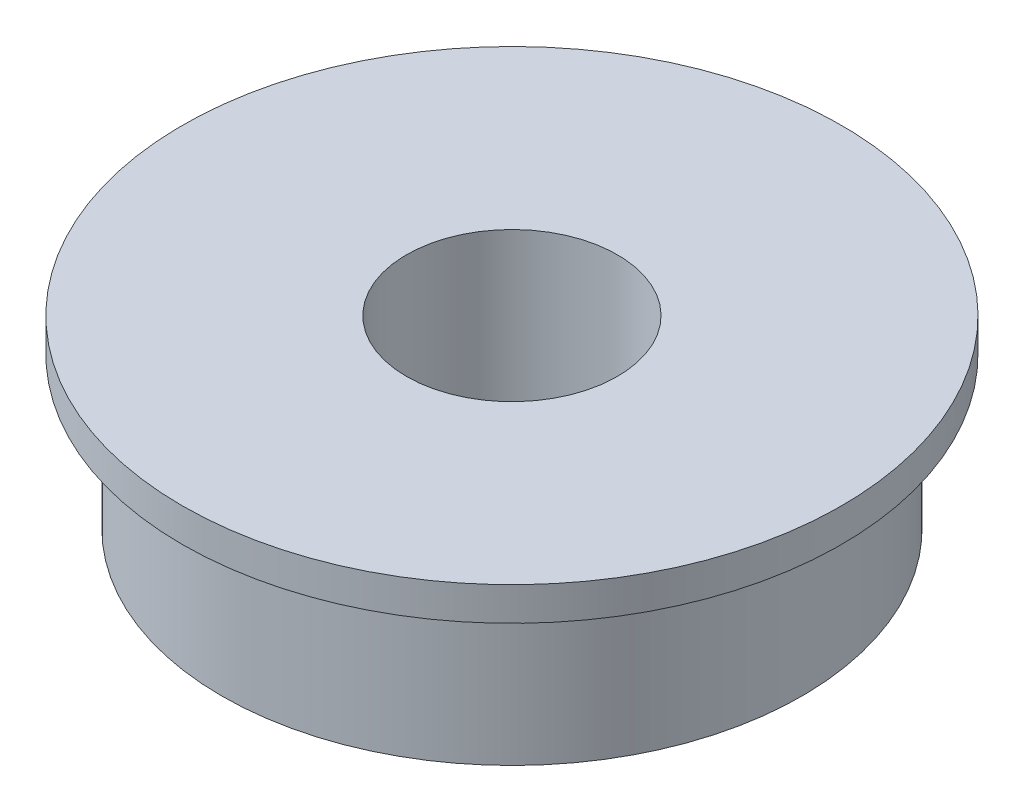
SolidWorks part; units mm, degrees
ref_plane "Front Plane" through (0, 0, 0) normal (0, 0, 1) x (1, 0, 0)
ref_plane "Top Plane" through (0, 0, 0) normal (0, 1, 0) x (1, 0, 0)
ref_plane "Right Plane" through (0, 0, 0) normal (1, 0, 0) x (0, 0, -1)
sketch "Sketch1" plane through (0, 0, 0) normal (0, 1, 0) x (1, 0, 0)
  circle A0 centre (0, 0) radius 4
  circle A1 centre (0, 0) radius 11
  dimension "D1" = 8
  dimension "D2" = 22
extrude "Boss-Extrude1" add sketch "Sketch1" along normal blind 7
sketch "Sketch2" plane through (0, 7, 0) normal (0, 1, 0) x (1, 0, 0)
  circle A0 centre (0, 0) radius 12.5
  circle A1 centre (0, 0) radius 11 construction
  circle A2 centre (0, 0) radius 11
  dimension "D1" = 25
extrude "Boss-Extrude2" add sketch "Sketch2" against normal blind 1.27
